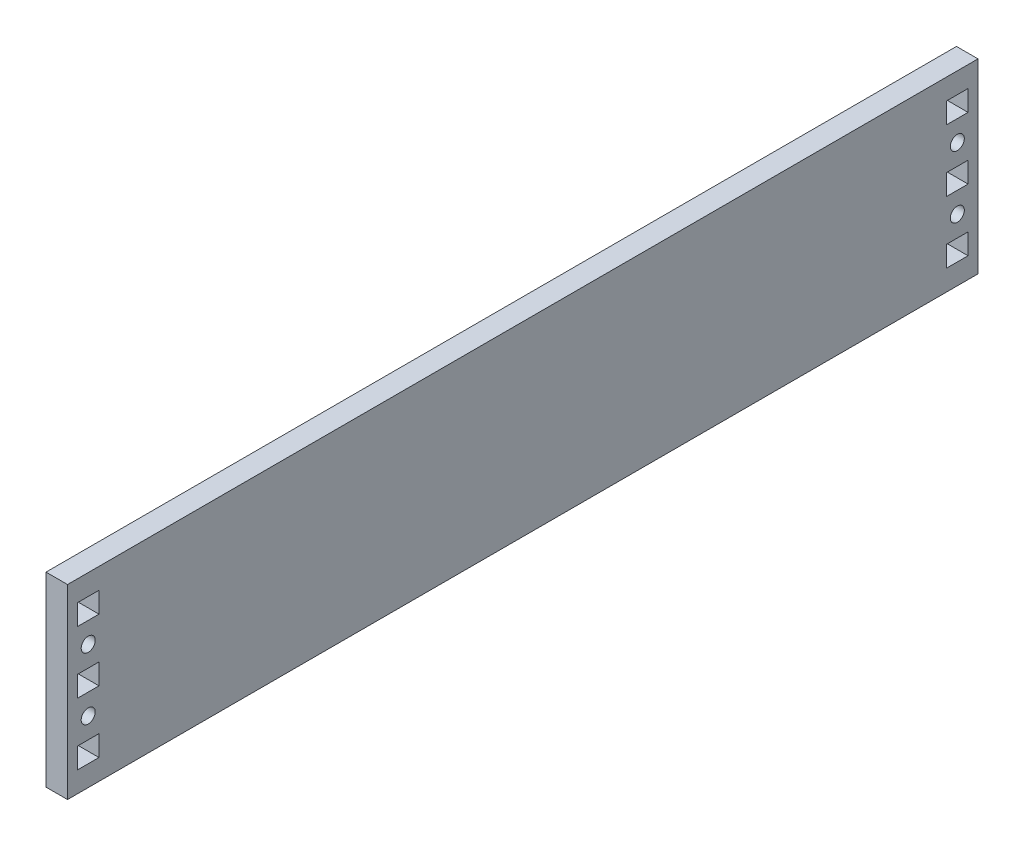
SolidWorks part; units mm, degrees
material "Acrylic (Medium-high impact)"
ref_plane "Front Plane" through (0, 0, 0) normal (0, 0, 1) x (1, 0, 0)
ref_plane "Top Plane" through (0, 0, 0) normal (0, 1, 0) x (1, 0, 0)
ref_plane "Right Plane" through (0, 0, 0) normal (1, 0, 0) x (0, 0, -1)
sketch "Sketch1" plane through (0, 0, 0) normal (1, 0, 0) x (0, 0, -1)
  line L0 (0, 0) -> (0, 28.575) construction
  line L1 (-139.7, 28.575) -> (139.7, 28.575)
  line L2 (-139.7, 28.575) -> (-139.7, -28.575)
  line L3 (-139.7, -28.575) -> (139.7, -28.575)
  line L4 (139.7, 28.575) -> (139.7, -28.575)
  line L5 (-130.048, 0) -> (0, 0) construction
  line L6 (0, 0) -> (130.048, 0) construction
  line L7 (0, 0) -> (0, -28.575) construction
  line B0 (-130.048, 3.175) -> (-130.048, -3.175)
  line B1 (-130.048, -3.175) -> (-136.652, -3.175)
  line B2 (-136.652, -3.175) -> (-136.652, 3.175)
  line B3 (-136.652, 3.175) -> (-130.048, 3.175)
  line B4 (-130.048, 22.225) -> (-130.048, 15.875)
  line B5 (-130.048, 15.875) -> (-136.652, 15.875)
  line B6 (-136.652, 15.875) -> (-136.652, 22.225)
  line B7 (-136.652, 22.225) -> (-130.048, 22.225)
  circle B8 centre (-133.35, 9.525) radius 2.1526
  line B9 (-130.048, -15.875) -> (-130.048, -22.225)
  line B10 (-130.048, -22.225) -> (-136.652, -22.225)
  line B11 (-136.652, -15.875) -> (-136.652, -22.225)
  line B12 (-130.048, -15.875) -> (-136.652, -15.875)
  circle B13 centre (-133.35, -9.525) radius 2.1527
  line B14 (136.652, 3.175) -> (136.652, -3.175)
  line B15 (136.652, -3.175) -> (130.048, -3.175)
  line B16 (130.048, -3.175) -> (130.048, 3.175)
  line B17 (130.048, 3.175) -> (136.652, 3.175)
  line B18 (136.652, 22.225) -> (136.652, 15.875)
  line B19 (136.652, 15.875) -> (130.048, 15.875)
  line B20 (130.048, 15.875) -> (130.048, 22.225)
  line B21 (130.048, 22.225) -> (136.652, 22.225)
  circle B22 centre (133.35, 9.525) radius 2.1526
  line B23 (136.652, -15.875) -> (136.652, -22.225)
  line B24 (136.652, -22.225) -> (130.048, -22.225)
  line B25 (130.048, -15.875) -> (130.048, -22.225)
  line B26 (136.652, -15.875) -> (130.048, -15.875)
  circle B27 centre (133.35, -9.525) radius 2.1527
  dimension "D1" = 266.7
  dimension "D2" = 57.15
  dimension "D3" = 6.35
  dimension "D4" = 6.35
sketch_block_instance "BOLT_HOLE_2X-1"
sketch_block "BOLT_HOLE_2X" parameters "D1"=4.3053, "D2"=6.35, "D3"=6.35, "D4"=6.604
sketch_block_instance "BOLT_HOLE_2X-2"
extrude "Boss-Extrude1" add sketch "Sketch1" along normal blind 6.604
